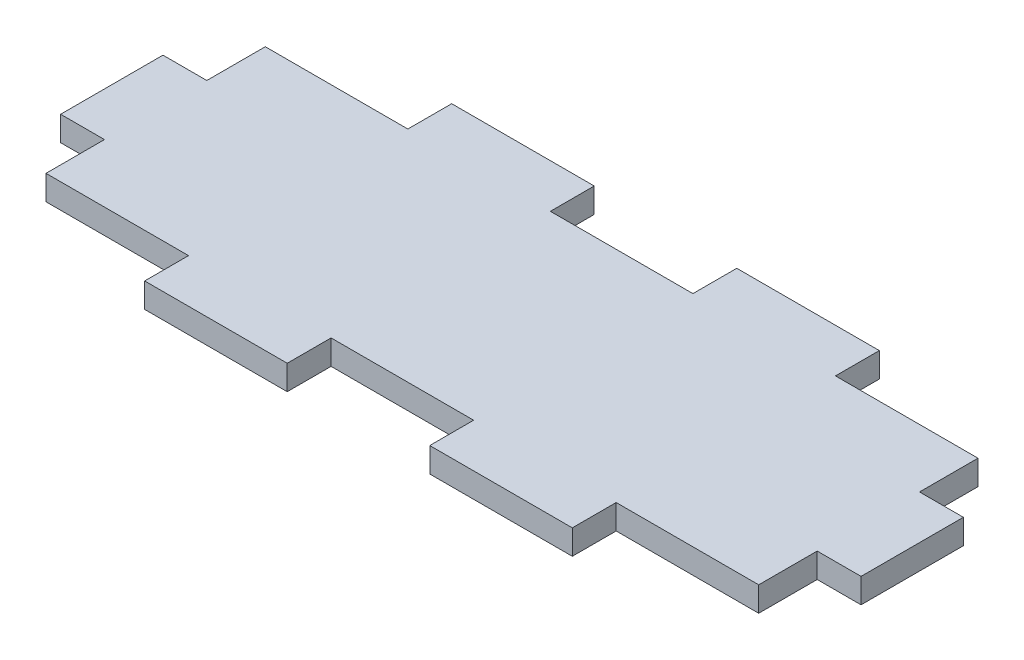
SolidWorks part; units mm, degrees
ref_plane "Front Plane" through (0, 0, 0) normal (0, 0, 1) x (1, 0, 0)
ref_plane "Top Plane" through (0, 0, 0) normal (0, 1, 0) x (1, 0, 0)
ref_plane "Right Plane" through (0, 0, 0) normal (1, 0, 0) x (0, 0, -1)
sketch "Sketch1" plane through (0, 0, 0) normal (0, 1, 0) x (1, 0, 0)
  line L0 (0, 10) -> (65, 10) construction
  line L1 (0, 0) -> (65, 0)
  line L2 (0, 0) -> (0, 20)
  line L3 (0, 20) -> (65, 20)
  line L4 (65, 0) -> (65, 20)
  line L5 (13, 20) -> (26, 20)
  line L6 (13, 20) -> (13, 24)
  line L7 (13, 24) -> (26, 24)
  line L8 (26, 20) -> (26, 24)
  line L9 (39, 20) -> (52, 20)
  line L10 (39, 20) -> (39, 24)
  line L11 (39, 24) -> (52, 24)
  line L12 (52, 20) -> (52, 24)
  line L13 (65, 14.6667) -> (69, 14.6667)
  line L14 (65, 14.6667) -> (65, 5.3333)
  line L15 (65, 5.3333) -> (69, 5.3333)
  line L16 (69, 14.6667) -> (69, 5.3333)
  line L17 (26, 24) -> (39, 24) construction
  line L18 (0, 14.6667) -> (-4, 14.6667)
  line L19 (0, 14.6667) -> (0, 5.3333)
  line L20 (0, 5.3333) -> (-4, 5.3333)
  line L21 (-4, 14.6667) -> (-4, 5.3333)
  line L22 (52, 24) -> (65, 24) construction
  line L23 (13, 24) -> (0, 24) construction
  line L24 (26, -4) -> (39, -4) construction
  line L25 (52, 0) -> (52, -4)
  line L26 (39, -4) -> (52, -4)
  line L27 (39, 0) -> (39, -4)
  line L28 (39, 0) -> (52, 0)
  line L29 (26, 0) -> (26, -4)
  line L30 (13, -4) -> (26, -4)
  line L31 (13, 0) -> (13, -4)
  line L32 (13, 0) -> (26, 0)
  line L33 (-4, 14.6667) -> (-4, 24) construction
  line L34 (-4, 5.3333) -> (-4, -4) construction
  point P23 (-4, 10)
  point P24 (69, 10)
  dimension "D1" = 20
  dimension "D2" = 65
  dimension "D3" = 4
extrude "Boss-Extrude1" add sketch "Sketch1" along normal blind 2.25 contours L1 L4 L3 L2 | L18 L21 L20 L2 | L1 L31 L30 L29 | L3 L8 L7 L6 | L3 L12 L11 L10 | L1 L27 L26 L25 | L16 L13 L4 L15
equation "\"D3@Sketch1\"=\"thick\"*2 + \"veneer_thickness\""
equation "\"D1@Boss-Extrude1\"=\"thick\"+\"veneer_thickness\""
equation "\"veneer_thickness\"= 0.5mm"
equation "\"thick\"= 1.75mm"
